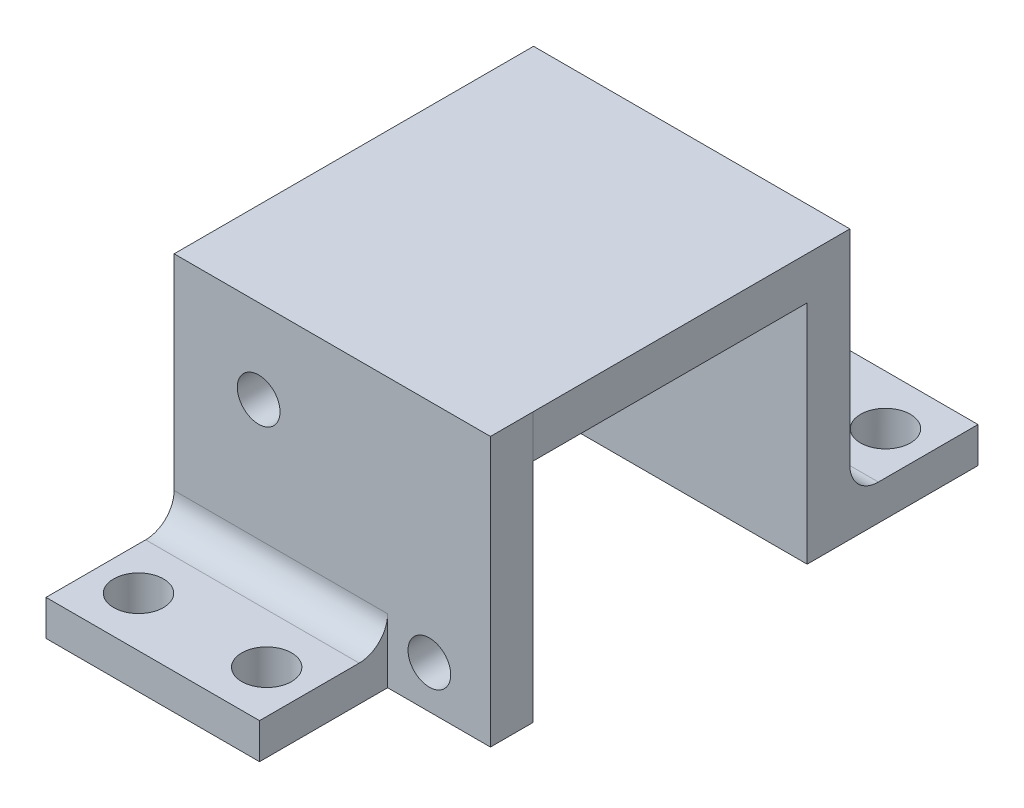
SolidWorks part; units mm, degrees
ref_plane "Front Plane" through (0, 0, 0) normal (0, 0, 1) x (1, 0, 0)
ref_plane "Top Plane" through (0, 0, 0) normal (0, 1, 0) x (1, 0, 0)
ref_plane "Right Plane" through (0, 0, 0) normal (1, 0, 0) x (0, 0, -1)
sketch "Sketch1" plane through (0, 0, 0) normal (0, 0, 1) x (1, 0, 0)
  line L1 (-11.11, 7.95) -> (11.11, 7.95)
  line L2 (-11.11, 7.95) -> (-11.11, -7.95)
  line L3 (-11.11, -7.95) -> (11.11, -7.95)
  line L4 (11.11, 7.95) -> (11.11, -7.95)
  line L5 (-11.11, 7.95) -> (11.11, -7.95) construction
  line L6 (-11.11, -7.95) -> (11.11, 7.95) construction
  circle A0 centre (-5.17, 5.05) radius 1.5
  circle A1 centre (6.82, -4.95) radius 1.5
  point P0 (0, 0)
  dimension "D3" = 3
  dimension "D6" = 4.29
  dimension "D8" = 3
  dimension "D1" = 22.22
  dimension "D2" = 15.9
  dimension "D4" = 2.9
  dimension "D5" = 5.94
  dimension "D7" = 3
extrude "Boss-Extrude1" add sketch "Sketch1" along normal blind 3
sketch "Sketch3" plane through (-11.11, 0, 0) normal (-1, 0, 0) x (0, 0, 1)
  line L0 (12, -5.45) -> (3, -5.45)
  line L1 (12, -5.45) -> (12, -7.95)
  line L2 (12, -7.95) -> (3, -7.95)
  line L3 (3, 7.95) -> (3, -7.95) construction
  line L4 (3, -5.45) -> (3, -7.95)
  dimension "D1" = 2.5
  dimension "D2" = 9
extrude "Boss-Extrude2" add sketch "Sketch3" against normal blind 15
fillet "Fillet2" radius 2 1 edges
sketch "Sketch5" plane through (0, -5.45, 0) normal (0, 1, 0) x (1, 0, 0)
  line L0 (-11.11, -8.5) -> (3.89, -8.5) construction
  line L1 (-11.11, -12) -> (-11.11, -5) construction
  line L2 (3.89, -12) -> (3.89, -5) construction
  line L3 (-3.61, -5) -> (-3.61, -12) construction
  line L4 (3.89, -5) -> (-11.11, -5) construction
  line L5 (3.89, -12) -> (-11.11, -12) construction
  circle A0 centre (-8.11, -8.5) radius 1.75
  circle A1 centre (0.89, -8.5) radius 1.75
  dimension "D1" = 3.5
  dimension "D2" = 3
extrude "Cut-Extrude1" cut sketch "Sketch5" against normal up to next
pattern_linear "LPattern2" count 2 spacing 6.95 along (0, 0, -1) of bodies 103
move or copy body "Body-Move/Copy3" bodies to move or copy 107 copy no rotation origin (0, 0, -13.1) rotation axis (0, 1, 0) rotation angle 180
sketch "Sketch11" plane through (-11.11, 0, 0) normal (-1, 0, 0) x (0, 0, 1)
  line L0 (-22.25, 7.95) -> (-22.25, 10.95)
  line L1 (0, 7.95) -> (0, 10.95)
  line L2 (0, 10.95) -> (-22.25, 10.95)
  line L3 (-22.25, 7.95) -> (0, 7.95)
  dimension "D1" = 3
extrude "Boss-Extrude3" add sketch "Sketch11" against normal up to vertex (22.22 mm away)
sketch "Sketch12" plane through (-11.11, 0, 0) normal (-1, 0, 0) x (0, 0, 1)
  line L0 (0, 7.95) -> (3, 7.95)
  line L1 (3, 7.95) -> (3, 10.95)
  line L2 (3, 10.95) -> (0, 10.95)
  line L3 (0, 10.95) -> (0, 7.95)
extrude "Boss-Extrude4" add sketch "Sketch12" against normal up to vertex (22.22 mm away)
